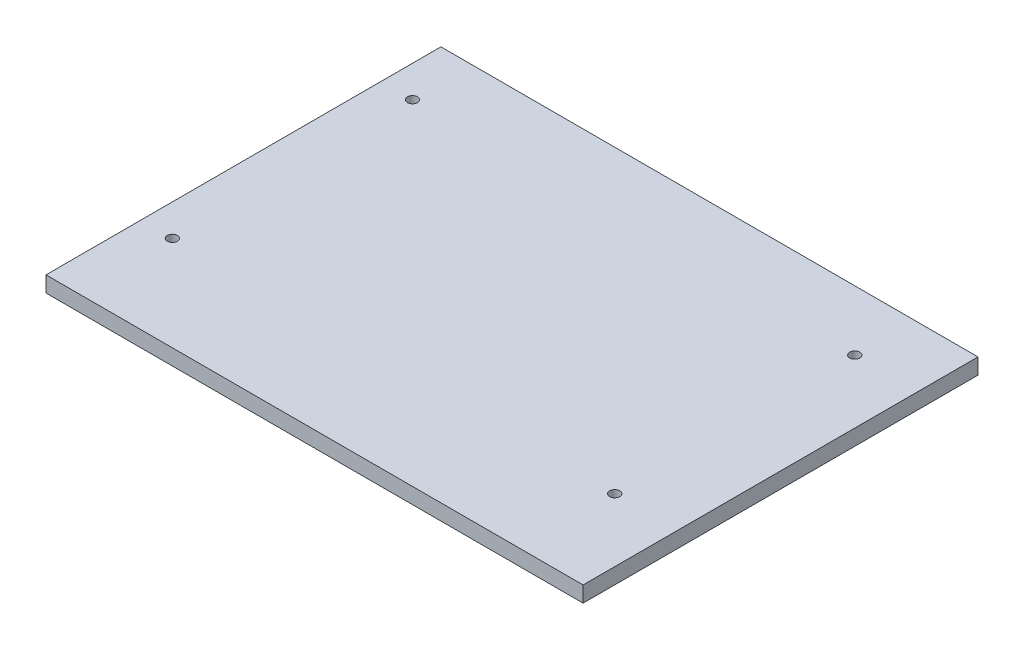
SolidWorks part; units mm, degrees
ref_plane "Front Plane" through (0, 0, 0) normal (0, 0, 1) x (1, 0, 0)
ref_plane "Top Plane" through (0, 0, 0) normal (0, 1, 0) x (1, 0, 0)
ref_plane "Right Plane" through (0, 0, 0) normal (1, 0, 0) x (0, 0, -1)
sketch "Sketch1" plane through (0, 0, 0) normal (0, 1, 0) x (1, 0, 0)
  line L1 (85, -62.5) -> (-85, -62.5)
  line L2 (85, -62.5) -> (85, 62.5)
  line L3 (85, 62.5) -> (-85, 62.5)
  line L4 (-85, -62.5) -> (-85, 62.5)
  line L5 (85, -62.5) -> (-85, 62.5) construction
  line L6 (85, 62.5) -> (-85, -62.5) construction
  circle A0 centre (-75, 43.5) radius 1.6
  circle A1 centre (-75, -32.5) radius 1.6
  circle A2 centre (65, -32.5) radius 1.6
  circle A3 centre (65, 43.5) radius 1.6
  point P0 (0, 0)
  point P14 (0, 0)
  dimension "D3" = 3.2
  dimension "D4" = 140
  dimension "D6" = 10
  dimension "D5" = 76
  dimension "D1" = 125
  dimension "D2" = 170
extrude "Boss-Extrude1" add sketch "Sketch1" along normal blind 5
